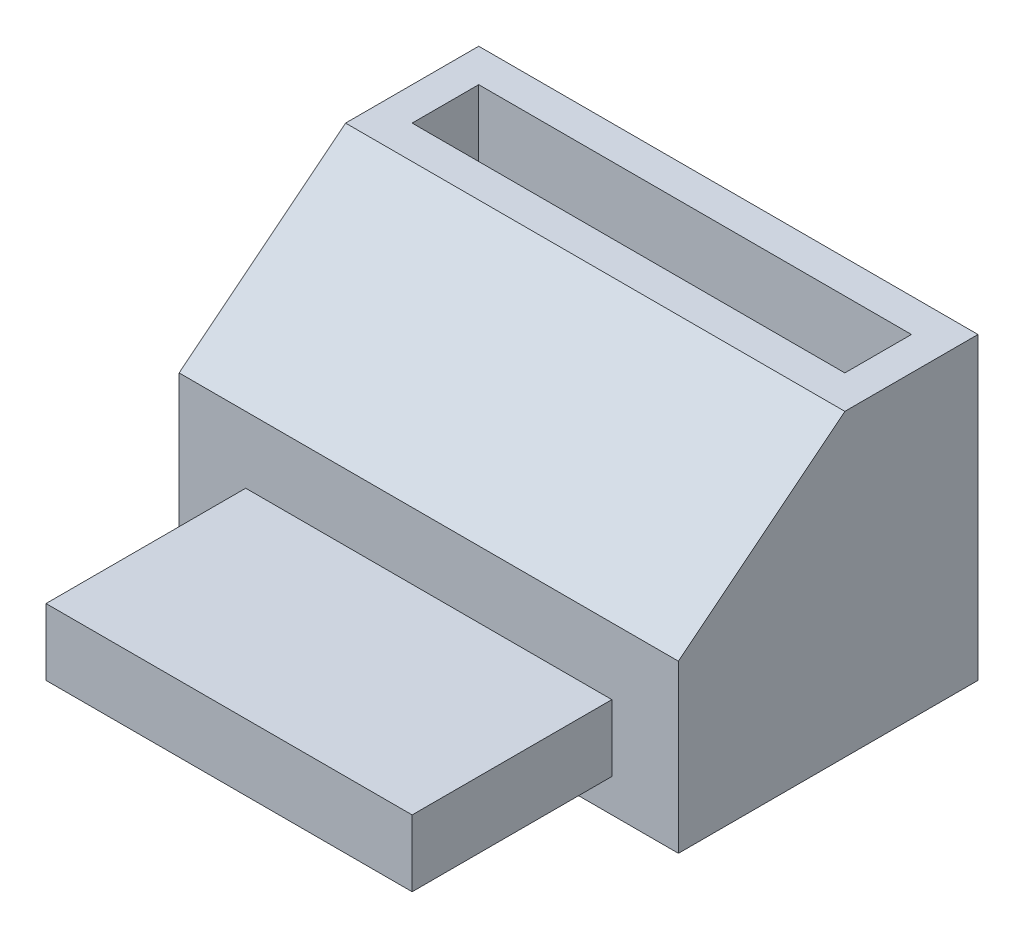
SolidWorks part; units mm, degrees
ref_plane "Front Plane" through (0, 0, 0) normal (0, 0, 1) x (1, 0, 0)
ref_plane "Top Plane" through (0, 0, 0) normal (0, 1, 0) x (1, 0, 0)
ref_plane "Right Plane" through (0, 0, 0) normal (1, 0, 0) x (0, 0, -1)
sketch "Sketch1" plane through (0, 0, 0) normal (1, 0, 0) x (0, 0, -1)
  line L0 (0, 0) -> (0, 90)
  line L1 (0, 90) -> (-40, 90)
  line L2 (-40, 90) -> (-90, 50)
  line L3 (-90, 50) -> (-90, 0)
  line L4 (-90, 0) -> (0, 0)
  dimension "D1" = 90
  dimension "D2" = 90
  dimension "D3" = 40
  dimension "D4" = 50
extrude "Boss-Extrude1" add sketch "Sketch1" along normal blind 150
sketch "Sketch2" plane through (0, 0, 90) normal (0, 0, 1) x (1, 0, 0)
  line L0 (150, 50) -> (0, 50) construction
  line L1 (20, 30) -> (130, 30)
  line L2 (20, 30) -> (20, 10)
  line L3 (20, 10) -> (130, 10)
  line L4 (130, 30) -> (130, 10)
  line L5 (150, 50) -> (150, 0) construction
  dimension "D1" = 110
  dimension "D2" = 20
  dimension "D3" = 20
  dimension "D4" = 20
extrude "Boss-Extrude2" add sketch "Sketch2" along normal blind 60
sketch "Sketch3" plane through (0, 90, 0) normal (0, 1, 0) x (1, 0, 0)
  line L0 (0, 0) -> (0, -40) construction
  line L1 (10, -10) -> (140, -10)
  line L2 (10, -10) -> (10, -30)
  line L3 (10, -30) -> (140, -30)
  line L4 (140, -10) -> (140, -30)
  line L5 (150, 0) -> (0, 0) construction
  dimension "D1" = 130
  dimension "D2" = 10
  dimension "D3" = 10
  dimension "D4" = 20
extrude "Cut-Extrude1" cut sketch "Sketch3" against normal blind 60
